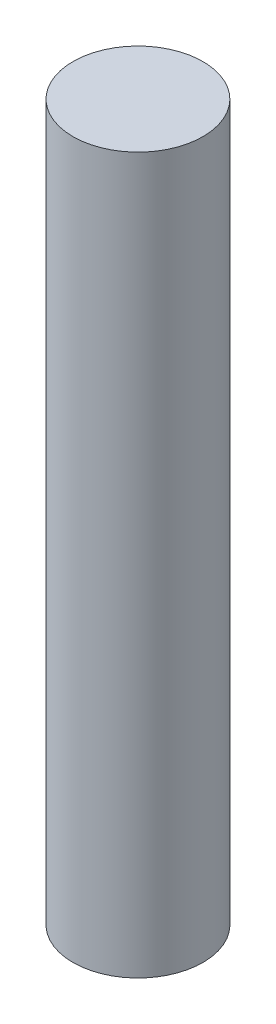
SolidWorks part; units mm, degrees
ref_plane "Front Plane" through (0, 0, 0) normal (0, 0, 1) x (1, 0, 0)
ref_plane "Top Plane" through (0, 0, 0) normal (0, 1, 0) x (1, 0, 0)
ref_plane "Right Plane" through (0, 0, 0) normal (1, 0, 0) x (0, 0, -1)
sketch "Sketch1" plane through (0, 0, 0) normal (0, 1, 0) x (1, 0, 0)
  circle A0 centre (0, 0) radius 3.175
  dimension "D1" = 6.35
extrude "Boss-Extrude1" add sketch "Sketch1" along normal blind 34.925
